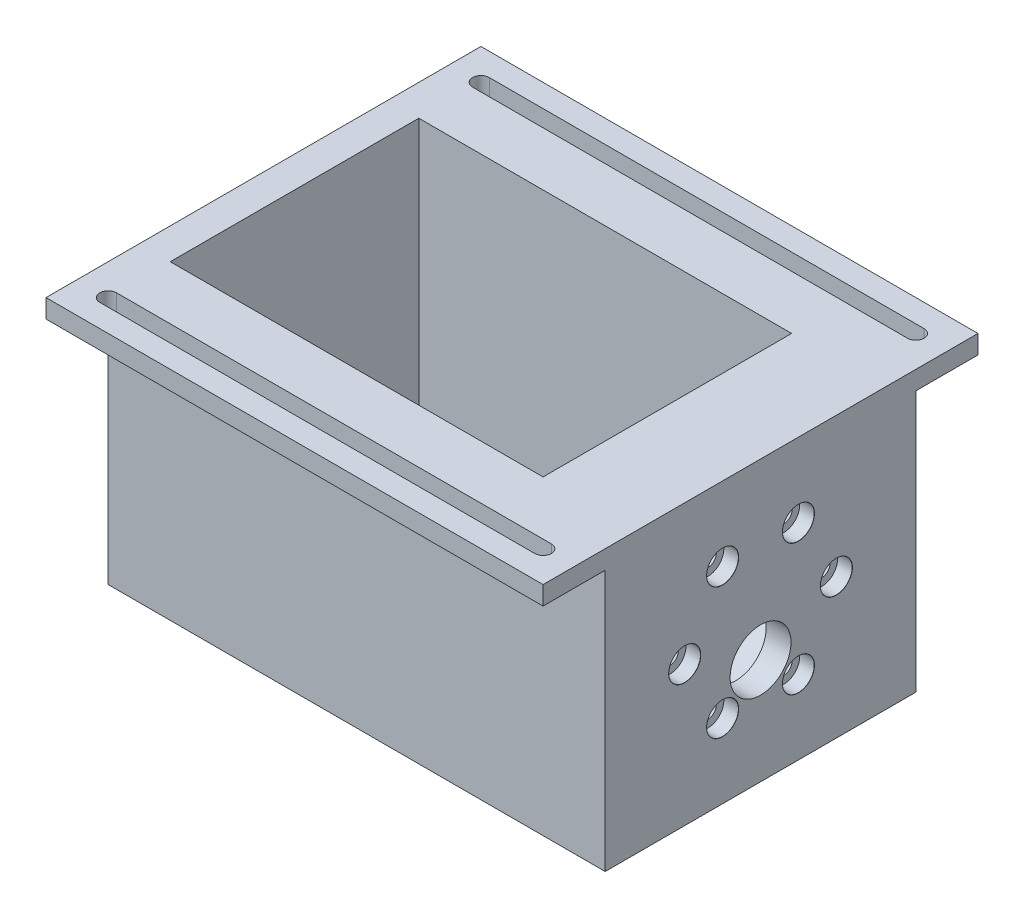
SolidWorks part; units mm, degrees
ref_plane "Front Plane" through (0, 0, 0) normal (0, 0, 1) x (1, 0, 0)
ref_plane "Top Plane" through (0, 0, 0) normal (0, 1, 0) x (1, 0, 0)
ref_plane "Right Plane" through (0, 0, 0) normal (1, 0, 0) x (0, 0, -1)
sketch "Sketch1" plane through (0, 0, 0) normal (0, 1, 0) x (1, 0, 0)
  line L1 (-50.8, -31.75) -> (50.8, -31.75)
  line L2 (-50.8, -31.75) -> (-50.8, 31.75)
  line L3 (-50.8, 31.75) -> (50.8, 31.75)
  line L4 (50.8, -31.75) -> (50.8, 31.75)
  line L5 (-50.8, -31.75) -> (50.8, 31.75) construction
  line L6 (-50.8, 31.75) -> (50.8, -31.75) construction
  point P0 (0, 0)
  dimension "D1" = 101.6
  dimension "D2" = 63.5
extrude "Boss-Extrude1" add sketch "Sketch1" along normal blind 57.15
sketch "Sketch2" plane through (50.8, 29.8204, 50.8942) normal (1, 0, 0) x (0, 0, -1)
  line L0 (19.1442, 27.3296) -> (19.1442, -29.8204) construction
  circle A0 centre (50.8942, -1.2454) radius 18.542
  point P6 (19.1442, -1.2454)
  dimension "D1" = 37.084
hole_wizard "CBORE for M3 SHCS1" positions "Sketch4" profile "Sketch6" counterbore size "M3" standard "ANSI Metric"
sketch "Sketch4" plane through (50.8, 62.23, 0) normal (-1, 0, 0) x (0, -1, 0)
  line L1 (5.08, 31.75) -> (62.23, 31.75) construction
  circle A0 centre (33.655, 0) radius 15.5 construction
  point P8 (33.655, 15.5)
  point P10 (47.0784, 7.75)
  point P11 (47.0784, -7.75)
  point P12 (33.655, -15.5)
  point P13 (20.2316, -7.75)
  point P14 (20.2316, 7.75)
  point P15 (33.655, 0)
  point P26 (33.655, 31.75)
  dimension "D1" = 30.9999
  dimension "D2" = 6
sketch "Sketch6" plane through (50.8, 41.9984, 7.75) normal (0, 1, 0) x (0, 0, -1)
  line L0 (0, 0) -> (0, 6.1015)
  line L1 (0, 6.1015) -> (1.7, 5.08)
  line L2 (1.7, 5.08) -> (1.7, 3)
  line L3 (1.7, 3) -> (3.25, 3)
  line L5 (3.25, 3) -> (3.25, 0.025)
  line L6 (3.25, 0.025) -> (3.275, 0)
  line L7 (3.275, 0) -> (0, 0)
  line L8 (-3.25, 0.025) -> (-3.275, 0) construction
  line L10 (0, 6.1015) -> (-1.7, 5.08) construction
  line L11 (0, -6.35) -> (0, 107.95) construction
  dimension "Hole Dia." = 3.4
  dimension "Hole Depth" = 5.08
  dimension "C'Bore Dia." = 6.5
  dimension "C'Bore Depth" = 3
  dimension "Near C'Sink Dia." = 6.55
  dimension "Near C'Sink Angle" = 90
  dimension "Drill Angle" = 118
sketch "Sketch8" plane through (50.8, 29.8204, 44.1336) normal (1, 0, 0) x (0, 0, 1)
  circle A0 centre (-44.1336, 1.2454) radius 7 construction
  circle A1 centre (-44.1336, 1.2454) radius 18.542 construction
  circle A3 centre (-44.1336, 8.2454) radius 6.223
  dimension "D1" = 14
  dimension "D2" = 12.446
extrude "Cut-Extrude1" cut sketch "Sketch8" against normal blind 50.8
sketch "Sketch9" plane through (0, 57.15, 0) normal (0, 1, 0) x (1, 0, 0)
  line L0 (-50.8, 31.75) -> (-50.8, -31.75) construction
  line L1 (-44.45, -25.4) -> (31.75, -25.4)
  line L2 (-44.45, -25.4) -> (-44.45, 25.4)
  line L3 (-44.45, 25.4) -> (31.75, 25.4)
  line L4 (31.75, -25.4) -> (31.75, 25.4)
  line L5 (50.8, 31.75) -> (-50.8, 31.75) construction
  line L6 (50.8, -18.542) -> (50.8, 18.542) construction
  line L7 (-50.8, -31.75) -> (50.8, -31.75) construction
  dimension "D1" = 6.35
  dimension "D2" = 6.35
  dimension "D3" = 19.05
  dimension "D4" = 6.35
extrude "Cut-Extrude2" cut sketch "Sketch9" against normal blind 53.34
extrude "Cut-Extrude3" cut sketch "Sketch2" along normal blind 13.97 from surface at -19.05 starting at face at (31.75, 30.48, 0)
sketch "Sketch10" plane through (0, 57.15, 0) normal (0, 1, 0) x (1, 0, 0)
  line L0 (50.8, -31.75) -> (50.8, 31.75) construction
  line L1 (-50.8, 31.75) -> (50.8, 31.75)
  line L2 (-50.8, 31.75) -> (-50.8, 44.45)
  line L3 (-50.8, 44.45) -> (50.8, 44.45)
  line L4 (50.8, 31.75) -> (50.8, 44.45)
  line L5 (-50.8, -31.75) -> (50.8, -31.75)
  line L6 (-50.8, -31.75) -> (-50.8, -44.45)
  line L7 (-50.8, -44.45) -> (50.8, -44.45)
  line L8 (50.8, -31.75) -> (50.8, -44.45)
  dimension "D1" = 12.7
  dimension "D2" = 12.7
extrude "Boss-Extrude2" add sketch "Sketch10" against normal blind 3.81
sketch "Sketch11" plane through (0, 57.15, 0) normal (0, 1, 0) x (1, 0, 0)
  line L0 (-44.45, 38.1) -> (44.45, 38.1) construction
  line L1 (-44.45, 39.8018) -> (44.45, 39.8018)
  line L2 (-44.45, 36.3982) -> (44.45, 36.3982)
  line L3 (0, 0) -> (67.8726, 0) construction
  line L4 (50.8, 44.45) -> (-50.8, 44.45) construction
  line L5 (-50.8, 44.45) -> (-50.8, -44.45) construction
  line L6 (50.8, -44.45) -> (50.8, 44.45) construction
  line L7 (-44.45, -38.1) -> (44.45, -38.1) construction
  line L8 (-44.45, -39.8018) -> (44.45, -39.8018)
  line L9 (-44.45, -36.3982) -> (44.45, -36.3982)
  arc A0 (-44.45, 39.8018) -> (-44.45, 36.3982) centre (-44.45, 38.1) ccw
  arc A1 (44.45, 36.3982) -> (44.45, 39.8018) centre (44.45, 38.1) ccw
  arc A2 (-44.45, -39.8018) -> (-44.45, -36.3982) centre (-44.45, -38.1) cw
  arc A3 (44.45, -36.3982) -> (44.45, -39.8018) centre (44.45, -38.1) cw
  point P2 (0, 38.1)
  point P18 (0, -38.1)
  dimension "D4" = 1.7018
  dimension "D1" = 6.35
  dimension "D2" = 6.35
  dimension "D3" = 6.35
extrude "Cut-Extrude4" cut sketch "Sketch11" against normal up to surface (3.81 mm away) up to face at (0, 53.34, 38.1)
